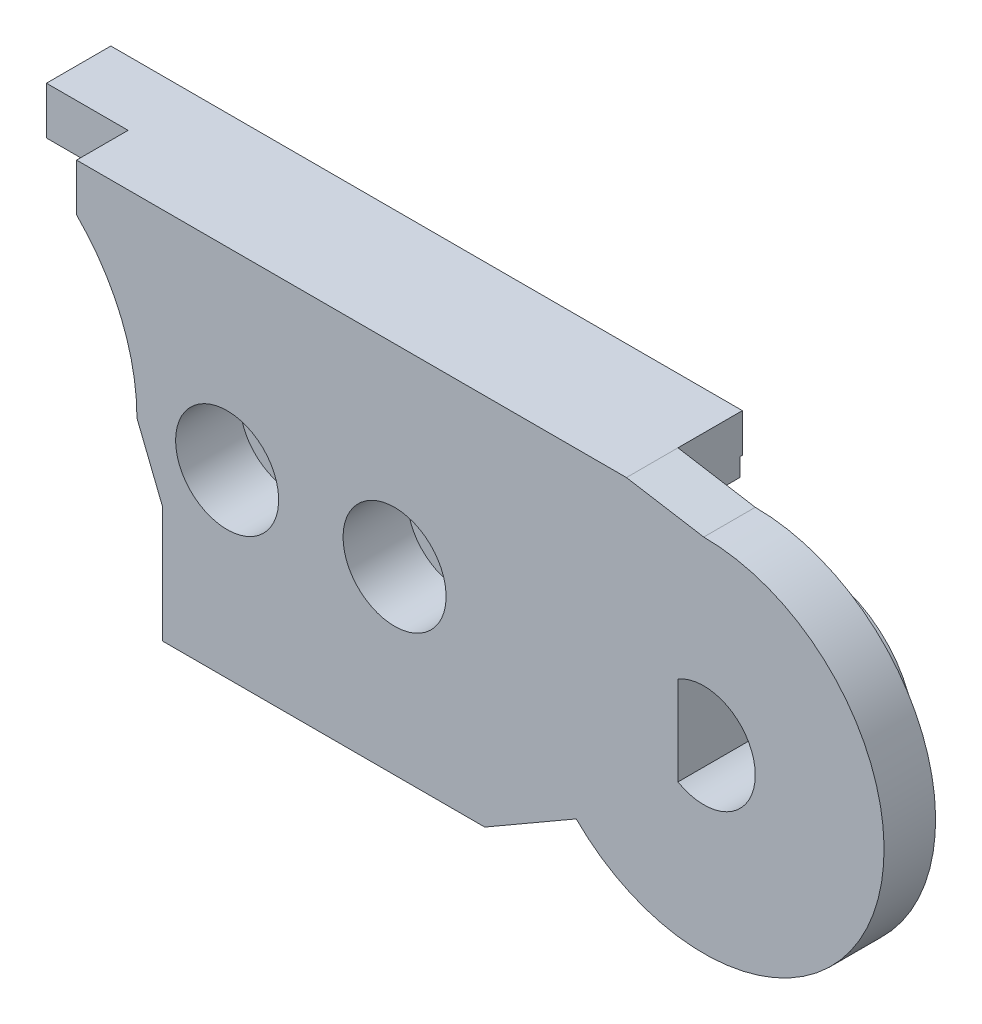
SolidWorks part; units mm, degrees
ref_plane "Front Plane" through (0, 0, 0) normal (0, 0, 1) x (1, 0, 0)
ref_plane "Top Plane" through (0, 0, 0) normal (0, 1, 0) x (1, 0, 0)
ref_plane "Right Plane" through (0, 0, 0) normal (1, 0, 0) x (0, 0, -1)
sketch "Sketch3" plane through (0, 0, 0) normal (0, 0, 1) x (1, 0, 0)
  line L7 (8, 0) -> (9, -2.5)
  line L11 (30, 7) -> (27, 7.5)
  line L13 (0, 7) -> (0, 7.5) construction
  line L14 (0, 7.5) -> (-22.3287, 7.5) construction
  line L15 (0, 5.3) -> (-14, 5.3) construction
  line L16 (0, 4) -> (-14, 4) construction
  line L17 (-14, 4) -> (-14, 5.3) construction
  line L18 (5.6569, 5.6569) -> (5.6569, 7.5)
  line L19 (5.6569, 7.5) -> (27, 7.5)
  line L20 (21.5, -7) -> (9, -7)
  line L21 (9, -7) -> (9, -2.5)
  line L23 (25.0503, -4.9497) -> (21.5, -7)
  arc A4 (8, 0) -> (5.6569, 5.6569) centre (0, 0) ccw
  arc A5 (25.0503, -4.9497) -> (30, 7) centre (30, 0) ccw
  circle A6 centre (0, 0) radius 7 construction
  circle A7 centre (0, 0) radius 3.9 construction
  circle A8 centre (0, 0) radius 5.3 construction
  circle A9 centre (0, 0) radius 4 construction
  dimension "D10" = 0.5
  dimension "D17" = 14
  dimension "D5" = 135
  dimension "D6" = 12.5
  dimension "D7" = 4.5
  dimension "D8" = 1
  dimension "D9" = 45
  dimension "D11" = 1.8431
  dimension "D12" = 30
  dimension "D14" = 3
extrude "Boss-Extrude1" add sketch "Sketch3" along normal blind 2 contours A5 L11 L19 L18 A4 L7 L21 L20 L23
sketch "Sketch20" plane through (0, 0, 0) normal (0, 0, 1) x (1, 0, 0)
  line L0 (0, 7) -> (0, 7.5) construction
  line L1 (0, 7.5) -> (-19.4737, 7.5) construction
  line L2 (0, 5.3) -> (-14, 5.3) construction
  line L3 (0, 4) -> (-14, 4) construction
  line L4 (-14, 4) -> (-14, 5.3) construction
  line L5 (0, 5.3) -> (17.4849, 5.3) construction
  line L6 (17.4849, 5.3) -> (17.4849, 4) construction
  line L7 (17.4849, 4) -> (0, 4) construction
  line L8 (-2.5, 7.5) -> (-2.5, 2.868) construction
  circle A0 centre (0, 0) radius 7 construction
  circle A1 centre (0, 0) radius 3.9 construction
  circle A3 centre (0, 0) radius 5.3 construction
  circle A4 centre (0, 0) radius 4 construction
  circle A5 centre (0, 0) radius 2 construction
  dimension "D1" = 0
  dimension "D2" = 2.5
ref_plane "Plane1" through (0, 0, 2) normal (0, 0, 1) x (1, 0, 0)
sketch "Sketch4" plane through (0, 0, 2) normal (0, 0, 1) x (1, 0, 0)
  line L4 (5.6569, 5.6569) -> (5.6569, 7.5)
  line L5 (5.6569, 5.6569) -> (5.6569, 7.5) construction
  line L6 (5.6569, 7.5) -> (21.5, 7.5)
  line L10 (8, 0) -> (9, -2.5)
  line L11 (9, -2.5) -> (9, -7)
  line L12 (9, -7) -> (21.5, -7)
  line L13 (21.5, -7) -> (21.5, 7.5)
  arc A0 (8, 0) -> (5.6569, 5.6569) centre (0, 0) ccw construction
  arc A3 (8, 0) -> (5.6569, 5.6569) centre (0, 0) ccw
sketch "Sketch22" plane through (0, 0, 2) normal (0, 0, 1) x (1, 0, 0)
  line L0 (5.6569, 5.6569) -> (2.4868, 5.6569)
  line L1 (5.6569, 7.5) -> (21.5, 7.5)
  line L2 (5.6569, 7.5) -> (2.4868, 7.5)
  line L3 (2.4868, 7.5) -> (2.4868, 5.6569)
  line L6 (8, 0) -> (9, -2.5)
  line L7 (9, -2.5) -> (9, -7)
  line L8 (9, -7) -> (21.5, -7)
  line L10 (21.5, 7.5) -> (27, 7.5)
  line L11 (27, 7.5) -> (27, 2.172)
  line L12 (27, 2.172) -> (23.2751, 2.172)
  line L13 (21.5, -7) -> (23.2751, -5.9749)
  line L14 (25.0503, -4.9497) -> (21.5, -7) construction
  line L15 (23.2751, -5.9749) -> (23.2751, 2.172)
  arc A0 (8, 0) -> (5.6569, 5.6569) centre (0, 0) ccw
extrude "Boss-Extrude6" add sketch "Sketch22" along normal blind 2.5
sketch "Sketch25" plane through (0, 0, 2) normal (0, 0, 1) x (1, 0, 0)
  line L0 (0, 5.3) -> (18.0981, 5.3) construction
  line L1 (0, 4) -> (18.0981, 4) construction
  line L2 (18.0981, 4) -> (18.0981, 5.3) construction
sketch "Sketch26" plane through (0, 0, 2) normal (0, 0, 1) x (1, 0, 0)
  line L1 (18.0981, 5.3) -> (2.5301, 5.3)
  line L2 (18.0981, 4) -> (2.5301, 4)
  line L3 (2.5301, 5.3) -> (2.5301, 4)
  line L4 (18.0981, 5.3) -> (27, 5.3)
  line L5 (27, 2.172) -> (27, 7.5) construction
  line L6 (27, 5.3) -> (27, 4)
  line L7 (27, 4) -> (18.0981, 4)
extrude "Cut-Extrude6" cut sketch "Sketch26" along normal blind 2.5
ref_plane "Plane18" through (0, 0, 4.5) normal (0, 0, 1) x (1, 0, 0)
sketch "Sketch31" plane through (0, 0, 4.5) normal (0, 0, 1) x (1, 0, 0)
  line L0 (2.4327, 5.6569) -> (0, 5.6569)
  line L4 (9, -5.6569) -> (0, -5.6569)
  line L5 (2.4327, 5.6569) -> (2.4868, 7.5)
  line L12 (9, -7) -> (9, -5.6569)
  line L13 (9, -2.5) -> (9, -7) construction
  line L16 (27, 7.5) -> (27, 2.172)
  line L17 (27, 2.172) -> (23.2751, 2.172)
  line L18 (23.2751, -5.9749) -> (23.2751, 2.172)
  line L19 (27, 7.5) -> (2.4868, 7.5)
  line L20 (9, -7) -> (21.5, -7)
  line L21 (21.5, -7) -> (23.2751, -5.9749)
  arc A0 (0, 5.6569) -> (0, -5.6569) centre (0, 0) ccw
  dimension "D1" = 5.6569
extrude "Boss-Extrude14" add sketch "Sketch31" along normal blind 2.3 separate body
sketch "Sketch32" plane through (0, 0, 6.8) normal (0, 0, 1) x (1, 0, 0)
  circle A0 centre (0, 0) radius 2.1
extrude "Cut-Extrude7" cut sketch "Sketch32" against normal blind 2.3
sketch "Sketch33" plane through (0, 0, 6.8) normal (0, 0, 1) x (1, 0, 0)
  line L4 (9, -5.6569) -> (9, -7)
  line L11 (9, -7) -> (21.5, -7)
  line L15 (21.5, -7) -> (21.5, -5.6569)
  line L16 (21.5, -5.6569) -> (9, -5.6569)
  line L17 (2.4868, 7.5) -> (21.5, 7.5)
  line L18 (27, 7.5) -> (2.4868, 7.5) construction
  line L19 (2.4868, 7.5) -> (2.4327, 5.6569)
  line L20 (2.4327, 5.6569) -> (21.5, 5.6569)
  line L21 (21.5, 5.6569) -> (21.5, 7.5)
extrude "Boss-Extrude15" add sketch "Sketch33" along normal blind 1.2
sketch "Sketch34" plane through (0, 0, 2) normal (0, 0, 1) x (1, 0, 0)
  line L0 (30, 5.3) -> (18.0981, 5.3) construction
  line L1 (30, 4) -> (18.0981, 4) construction
  circle A0 centre (30, 0) radius 2 construction
  circle A1 centre (30, 0) radius 5.3 construction
  circle A2 centre (30, 0) radius 4 construction
sketch "Sketch35" plane through (0, 0, 6.8) normal (0, 0, 1) x (1, 0, 0)
  line L0 (27, 2.172) -> (27, 6)
  line L1 (27, 2.172) -> (21.5204, 2.172)
  line L2 (27, 6) -> (21.5204, 6)
  line L3 (21.5204, 2.172) -> (21.5204, 6)
  line L4 (27, 2.172) -> (27, 7.5) construction
extrude "Cut-Extrude8" cut sketch "Sketch35" against normal blind 2.4
sketch "Sketch36" plane through (0, 0, 4.4) normal (0, 0, 1) x (1, 0, 0)
  line L0 (27, 2.172) -> (27, 4)
  line L1 (27, 2.172) -> (23.3, 2.172)
  line L2 (27, 4) -> (23.3, 4)
  line L3 (23.3, 2.172) -> (23.3, 4)
  line L4 (21.5, -7) -> (21.5, 7.5) construction
  dimension "D1" = 1.8
extrude "Cut-Extrude9" cut sketch "Sketch36" against normal blind 2.4
sketch "Sketch37" plane through (0, 0, 2) normal (0, 0, 1) x (1, 0, 0)
  circle A0 centre (30, 0) radius 3.9
extrude "Boss-Extrude16" add sketch "Sketch37" along normal blind 2.3
sketch "Sketch39" plane through (0, 0, 4.3) normal (0, 0, 1) x (1, 0, 0)
  line L0 (29, 1.7321) -> (29, -1.7321)
  arc A0 (29, -1.7321) -> (29, 1.7321) centre (30, 0) ccw
  dimension "D2" = 4
  dimension "D1" = 1
extrude "Cut-Extrude10" cut sketch "Sketch39" against normal through all
sketch "Sketch43" plane through (0, 0, 6.8) normal (0, 0, 1) x (1, 0, 0)
  line L2 (0, -5.6569) -> (9, -5.6569) construction
  circle A0 centre (11.5, 0) radius 2.5
  circle A1 centre (18, 0) radius 2.5
  dimension "D1" = 2.5
  dimension "D3" = 5
  dimension "D4" = 6.5
  dimension "D2" = 5.6569
extrude "Boss-Extrude17" add sketch "Sketch43" along normal blind 1.2
sketch "Sketch44" plane through (0, 0, 8) normal (0, 0, 1) x (1, 0, 0)
  circle A0 centre (11.5, 0) radius 0.95
  circle A1 centre (18, 0) radius 0.95
  dimension "D1" = 1.9
  dimension "D2" = 1.9
extrude "Cut-Extrude11" cut sketch "Sketch44" against normal through all
sketch "Sketch45" plane through (0, 0, 0) normal (0, 0, -1) x (-1, 0, 0)
  circle A0 centre (-11.5, 0) radius 2
  circle A1 centre (-18, 0) radius 2
extrude "Cut-Extrude12" cut sketch "Sketch45" against normal blind 2.5
ref_plane "Plane17" through (0, 0, 8) normal (0, 0, 1) x (1, 0, 0)
sketch "Sketch48" plane through (0, 0, 2) normal (0, 0, 1) x (1, 0, 0)
  circle A0 centre (30, 0) radius 5 construction
sketch "Sketch51" plane through (0, 0, 8) normal (0, 0, 1) x (1, 0, 0)
  line L0 (18.2355, 5.6569) -> (27.0112, -4.8677) construction
  line L1 (2.4327, 5.6569) -> (21.5, 5.6569) construction
sketch "Sketch52" plane through (0, 5.6569, 0) normal (0, -1, 0) x (1, 0, 0)
  circle A0 centre (18.2355, 8) radius 0.75
extrude "Cut-Extrude13" cut sketch "Sketch52" along direction (0.6404, -0.768, 0) on the side against the normal blind 10
mirror "Mirror1" about plane through (0, 0, 8) normal (0, 0, 1) of bodies 133 129
split "Split1" trim tools "Plane17" bodies to split 135 134 resulting bodies 136 137
delete or keep bodies "Body-Delete/Keep 1" type delete bodies bodies 129 133 137
